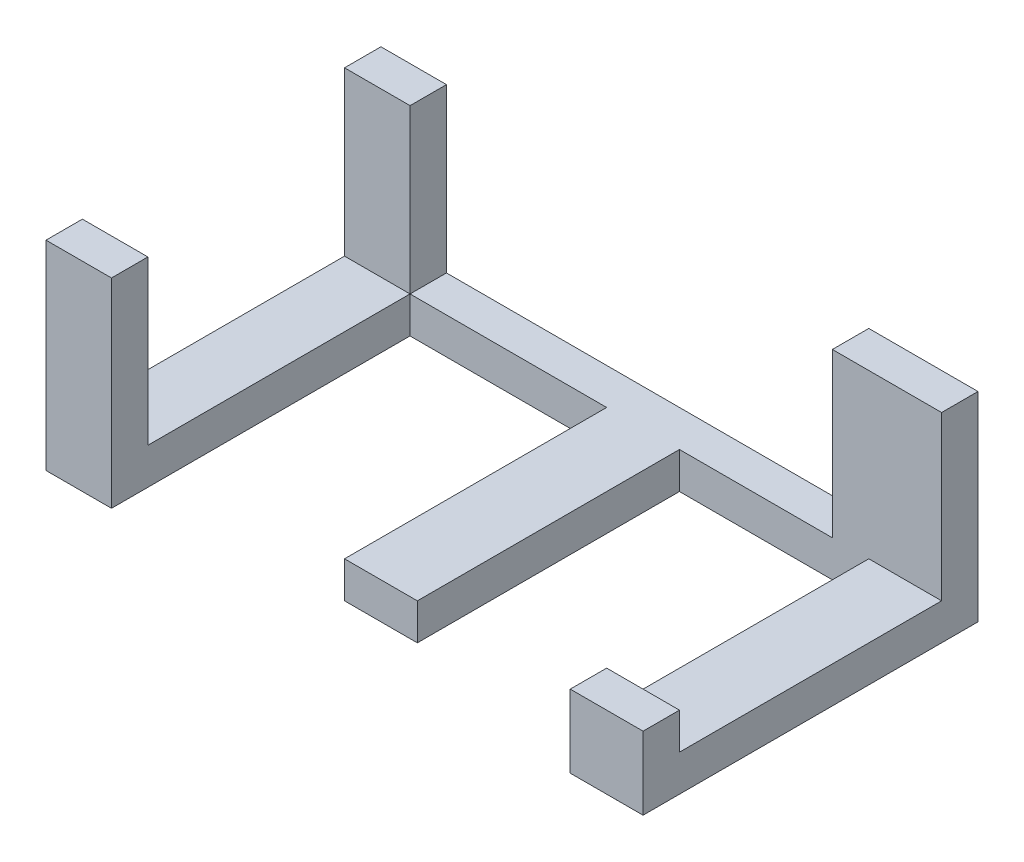
SolidWorks part; units mm, degrees
ref_plane "Alzado" through (0, 0, 0) normal (0, 0, 1) x (1, 0, 0)
ref_plane "Planta" through (0, 0, 0) normal (0, 1, 0) x (1, 0, 0)
ref_plane "Vista lateral" through (0, 0, 0) normal (1, 0, 0) x (0, 0, -1)
sketch "Croquis1" plane through (0, 0, 0) normal (0, 0, 1) x (1, 0, 0)
  line L0 (-58.7725, -23.4519) -> (23.2275, -23.4519)
  line L1 (-58.7725, -23.4519) -> (-58.7725, -28.4519)
  line L2 (-58.7725, -28.4519) -> (23.2275, -28.4519)
  line L3 (23.2275, -28.4519) -> (23.2275, -23.4519)
  dimension "D1" = 5
extrude "Saliente-Extruir1" add sketch "Croquis1" along normal blind 5
sketch "Croquis2" plane through (0, -23.4519, 0) normal (0, 1, 0) x (1, 0, 0)
  line L0 (23.2275, 0) -> (8.2275, 0)
  line L1 (23.2275, 0) -> (-58.7725, 0) construction
  line L2 (23.2275, -5) -> (23.2275, 0) construction
  line L3 (8.2275, 0) -> (8.2275, -5)
  line L4 (23.2275, -5) -> (-58.7725, -5) construction
  line L5 (8.2275, -5) -> (23.2275, -5)
  line L6 (23.2275, -5) -> (23.2275, 0)
  line L7 (-58.7725, 0) -> (-49.7725, 0)
  line L8 (-58.7725, -5) -> (-58.7725, 0) construction
  line L9 (-49.7725, 0) -> (-49.7725, -5)
  line L10 (-49.7725, -5) -> (-58.7725, -5)
  line L11 (-58.7725, -5) -> (-58.7725, 0)
extrude "Saliente-Extruir2" add sketch "Croquis2" along normal blind 22.4
sketch "Croquis3" plane through (0, 0, 5) normal (0, 0, 1) x (1, 0, 0)
  line L0 (-58.7725, -28.4519) -> (-49.779, -28.4519)
  line L1 (-58.7725, -28.4519) -> (23.2275, -28.4519) construction
  line L4 (-58.7725, -1.0519) -> (-58.7725, -28.4519) construction
  line L5 (23.2275, -28.4519) -> (23.2275, -1.0519) construction
  line L6 (23.2275, -23.4519) -> (23.2275, -28.4519)
  line L7 (23.2275, -23.4519) -> (13.2275, -23.4519)
  line L8 (13.2275, -23.4519) -> (13.2275, -28.4519)
  line L9 (13.2275, -28.4519) -> (23.2275, -28.4519)
  line L10 (23.2275, -28.4519) -> (23.0562, -28.3651)
  line L11 (-49.779, -28.4519) -> (-49.779, -23.4519)
  line L12 (8.2275, -23.4519) -> (-49.7725, -23.4519) construction
  line L13 (-49.779, -23.4519) -> (-58.7725, -23.4519)
  line L14 (-58.7725, -23.4519) -> (-58.7725, -28.4519)
  line L15 (-58.7725, -28.4519) -> (-22.7725, -28.4519)
  line L16 (-12.7725, -23.4519) -> (-22.7725, -23.4519)
  line L19 (-12.7725, -23.4519) -> (-12.7725, -28.4519)
  line L20 (-12.7725, -28.4519) -> (-22.7725, -28.4519)
  line L21 (-22.7725, -28.4519) -> (-22.7725, -23.4519)
  dimension "D1" = 5
extrude "Saliente-Extruir3" add sketch "Croquis3" along normal blind 36
sketch "Croquis4" plane through (0, 0, 41) normal (0, 0, 1) x (1, 0, 0)
  line L0 (-58.7725, -28.4519) -> (-58.7725, -1.0519)
  line L1 (-58.7725, -1.0519) -> (-49.7725, -1.0519)
  line L2 (-49.779, -28.4519) -> (-49.779, -1.0519)
  line L3 (-49.779, -1.0519) -> (-49.7725, -1.0519)
  line L4 (23.2275, -28.4519) -> (23.2275, -18.4519)
  line L5 (13.2275, -28.4519) -> (13.2275, -18.4519)
  line L6 (13.2275, -18.4519) -> (23.2275, -18.4519)
  line L7 (23.2275, -18.4519) -> (23.0363, -18.4687)
  line L8 (23.2275, -28.4519) -> (13.2275, -28.4519)
  line L9 (13.2275, -28.4519) -> (13.1687, -28.4929)
  line L10 (-49.779, -28.4519) -> (-58.7725, -28.4519)
  dimension "D1" = 10
extrude "Saliente-Extruir4" add sketch "Croquis4" along normal blind 5
